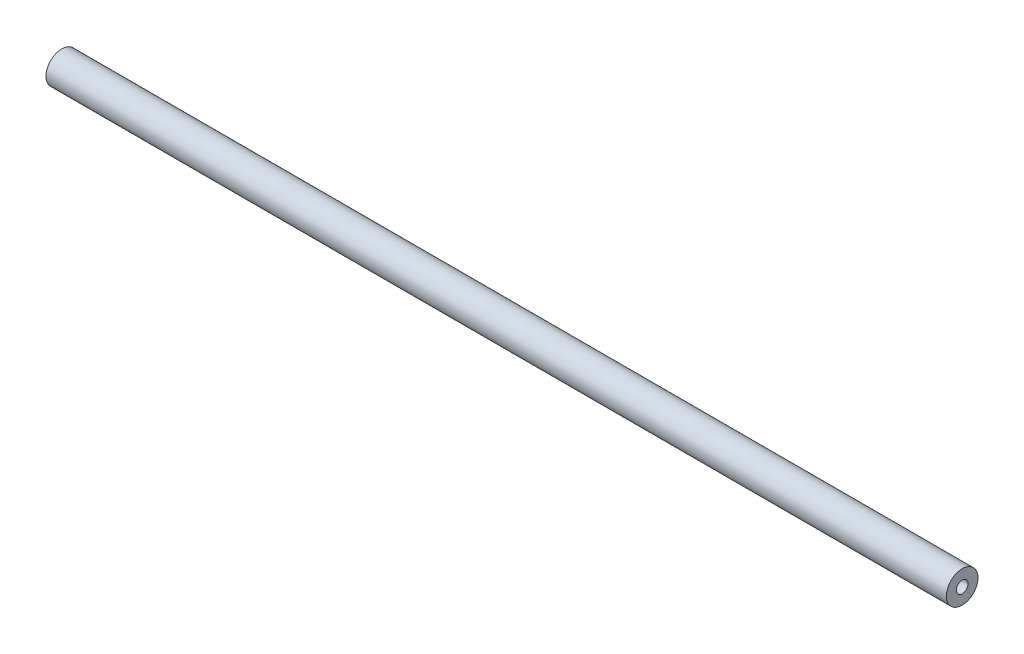
SolidWorks part; units mm, degrees
material "Cast Carbon Steel"
ref_plane "Front Plane" through (0, 0, 0) normal (0, 0, 1) x (1, 0, 0)
ref_plane "Top Plane" through (0, 0, 0) normal (0, 1, 0) x (1, 0, 0)
ref_plane "Right Plane" through (0, 0, 0) normal (1, 0, 0) x (0, 0, -1)
sketch "Sketch1" plane through (0, 0, 0) normal (1, 0, 0) x (0, 0, -1)
  circle A0 centre (0, 0) radius 12.7
  circle A1 centre (0, 0) radius 4.7625
  dimension "D1" = 25.4
  dimension "D2" = 7.9375
extrude "Boss-Extrude1" add sketch "Sketch1" along normal blind 723.9
